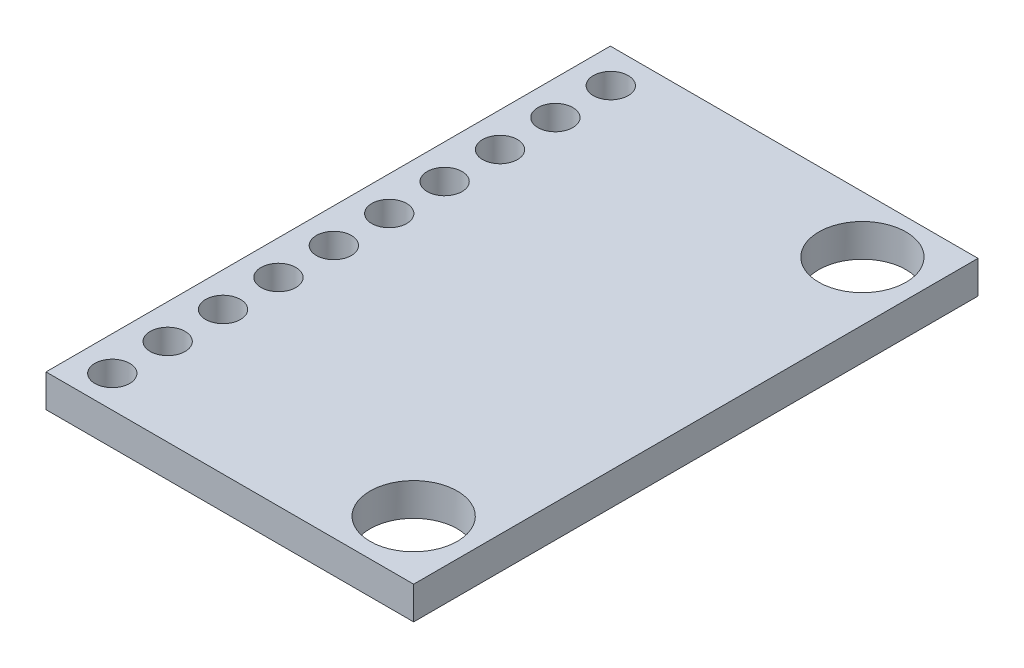
SolidWorks part; units mm, degrees
ref_plane "Front Plane" through (0, 0, 0) normal (0, 0, 1) x (1, 0, 0)
ref_plane "Top Plane" through (0, 0, 0) normal (0, 1, 0) x (1, 0, 0)
ref_plane "Right Plane" through (0, 0, 0) normal (1, 0, 0) x (0, 0, -1)
sketch "Sketch1" plane through (0, 0, 0) normal (0, 1, 0) x (1, 0, 0)
  line L1 (0, 0) -> (16.86, 0)
  line L2 (0, 0) -> (0, 25.88)
  line L3 (0, 25.88) -> (16.86, 25.88)
  line L4 (16.86, 0) -> (16.86, 25.88)
  dimension "D1" = 25.88
  dimension "D2" = 16.86
extrude "Boss-Extrude1" add sketch "Sketch1" along normal blind 1.5
sketch "Sketch2" plane through (0, 1.5, 0) normal (0, 1, 0) x (1, 0, 0)
  line L0 (16.86, 25.88) -> (0, 25.88) construction
  line L1 (16.86, 0) -> (16.86, 25.88) construction
  line L2 (0, 0) -> (16.86, 0) construction
  circle A0 centre (14.16, 23.28) radius 2
  circle A1 centre (14.16, 2.7) radius 2
  dimension "D1" = 4
  dimension "D2" = 2.6
  dimension "D3" = 2.7
  dimension "D4" = 2.7
extrude "Cut-Extrude1" cut sketch "Sketch2" against normal up to next
sketch "Sketch3" plane through (0, 1.5, 0) normal (0, 1, 0) x (1, 0, 0)
  line L0 (16.86, 25.88) -> (0, 25.88) construction
  line L1 (0, 25.88) -> (0, 0) construction
  circle A0 centre (1.58, 24.32) radius 0.8
  circle A1 centre (1.58, 21.78) radius 0.8
  circle A2 centre (1.58, 19.24) radius 0.8
  circle A3 centre (1.58, 16.7) radius 0.8
  circle A4 centre (1.58, 14.16) radius 0.8
  circle A5 centre (1.58, 11.62) radius 0.8
  circle A6 centre (1.58, 9.08) radius 0.8
  circle A7 centre (1.58, 6.54) radius 0.8
  circle A8 centre (1.58, 4) radius 0.8
  circle A9 centre (1.58, 1.46) radius 0.8
  dimension "D1" = 1.6
  dimension "D2" = 1.56
  dimension "D3" = 1.58
  dimension "D4" = 10
extrude "Cut-Extrude2" cut sketch "Sketch3" against normal up to next
